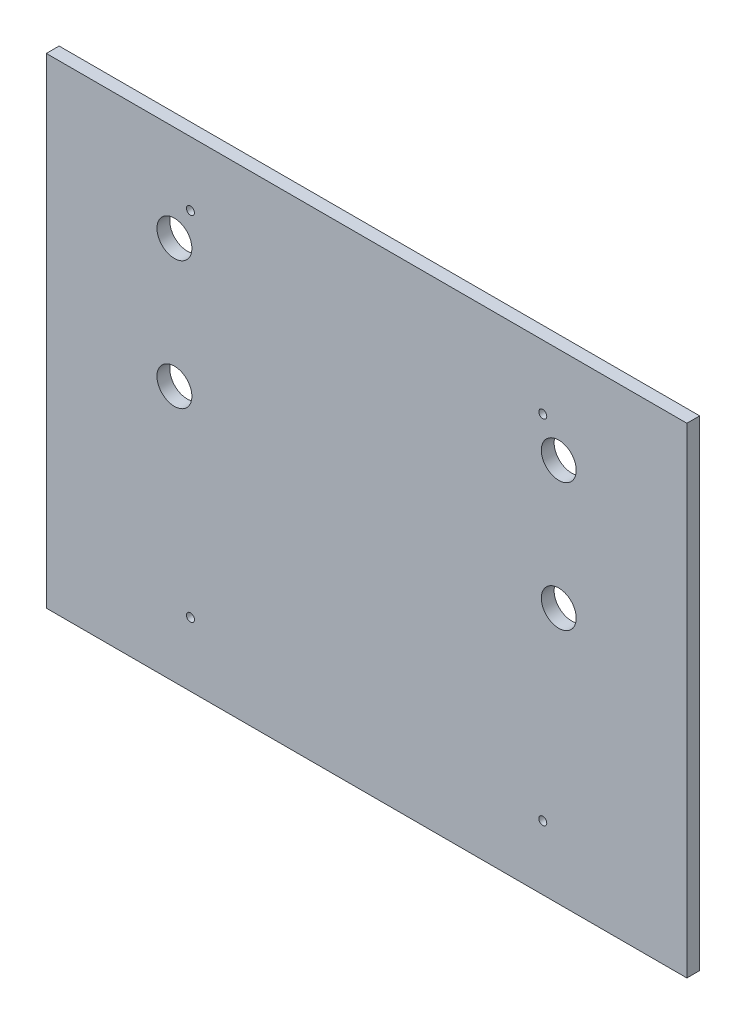
SolidWorks part; units mm, degrees
ref_plane "前视基准面" through (0, 0, 0) normal (0, 0, 1) x (1, 0, 0)
ref_plane "上视基准面" through (0, 0, 0) normal (0, 1, 0) x (1, 0, 0)
ref_plane "右视基准面" through (0, 0, 0) normal (1, 0, 0) x (0, 0, -1)
sketch "草图1" plane through (0, 0, 0) normal (0, 0, 1) x (1, 0, 0)
  line L0 (-55.6021, 34.2026) -> (344.3979, 34.2026)
  line L1 (-55.6021, 34.2026) -> (-55.6021, -265.7974)
  line L2 (-55.6021, -265.7974) -> (344.3979, -265.7974)
  line L3 (344.3979, -265.7974) -> (344.3979, 34.2026)
  circle A0 centre (24.3979, -25.7974) radius 10.9
  circle A1 centre (264.3979, -25.7974) radius 10.9
  circle A4 centre (254.3979, -5.7974) radius 2.5
  circle A5 centre (34.3979, -5.7974) radius 2.5
  circle A6 centre (34.3979, -225.7974) radius 2.5
  circle A7 centre (254.3979, -225.7974) radius 2.5
  circle A8 centre (24.3979, -105.7974) radius 10.9
  circle A9 centre (264.3979, -105.7974) radius 10.9
extrude "凸台-拉伸1" add sketch "草图1" along normal blind 8
